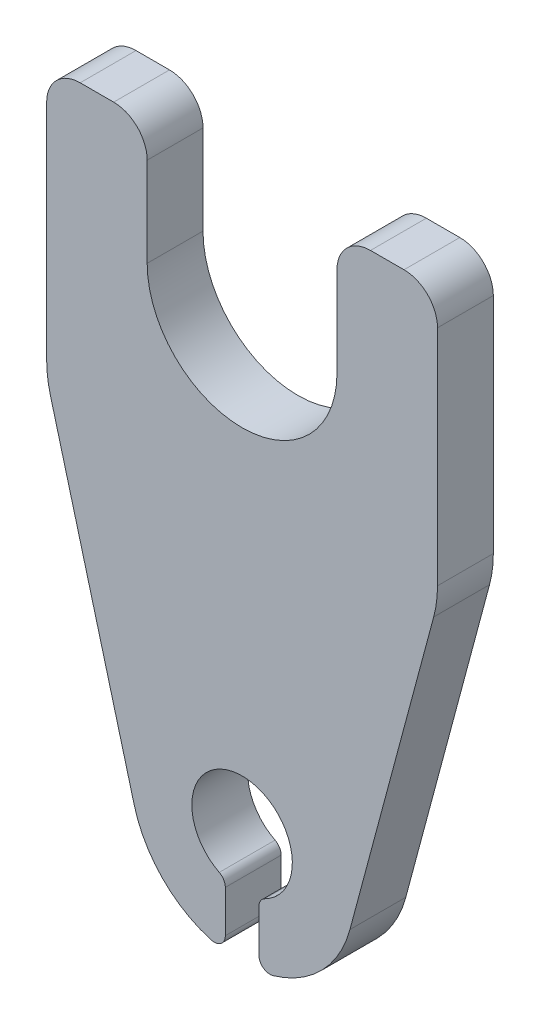
SolidWorks part; units mm, degrees
ref_plane "Plane1" through (0, 0, 0) normal (0, 0, 1) x (1, 0, 0)
ref_plane "Plane2" through (0, 0, 0) normal (0, 1, 0) x (1, 0, 0)
ref_plane "Plane3" through (0, 0, 0) normal (1, 0, 0) x (0, 0, -1)
sketch "Sketch1" plane through (0, 0, 0) normal (0, 0, 1) x (1, 0, 0)
  line L0 (0, 0) -> (0, 40) construction
  line L1 (1.5, -4.899) -> (1.5, -8.6458)
  line L2 (-1.5, -4.899) -> (-1.5, -8.6458)
  line L3 (8.5, 40) -> (8.5, 48)
  line L4 (11.5, 51) -> (14.5, 51)
  line L5 (-11.5, 51) -> (-14.5, 51)
  line L6 (-8.5, 40) -> (-8.5, 48)
  line L8 (17.5, 48) -> (17.5, 27.9904)
  line L9 (17.1593, 25.4022) -> (9.6593, -2.5882)
  line L10 (-17.1593, 25.4022) -> (-9.6593, -2.5882)
  line L11 (-17.5, 48) -> (-17.5, 27.9904)
  arc A0 (2.0455, -4.0083) -> (-2.0455, -4.0083) centre (0, 0) ccw
  arc A1 (2.7778, -9.6065) -> (9.6593, -2.5882) centre (0, 0) ccw
  arc A2 (-8.5, 40) -> (8.5, 40) centre (0, 40) ccw
  arc A3 (-9.6593, -2.5882) -> (-2.7778, -9.6065) centre (0, 0) ccw
  arc A4 (11.5, 51) -> (8.5, 48) centre (11.5, 48) ccw
  arc A5 (-8.5, 48) -> (-11.5, 51) centre (-11.5, 48) ccw
  arc A6 (-17.5, 48) -> (-14.5, 51) centre (-14.5, 48) cw
  arc A7 (17.5, 48) -> (14.5, 51) centre (14.5, 48) ccw
  arc A10 (-17.5, 27.9904) -> (-17.1593, 25.4022) centre (-7.5, 27.9904) ccw
  arc A11 (17.1593, 25.4022) -> (17.5, 27.9904) centre (7.5, 27.9904) ccw
  arc A12 (2.7778, -9.6065) -> (1.5, -8.6458) centre (2.5, -8.6458) cw
  arc A13 (2.0455, -4.0083) -> (1.5, -4.899) centre (2.5, -4.899) ccw
  arc A14 (-2.0455, -4.0083) -> (-1.5, -4.899) centre (-2.5, -4.899) cw
  arc A15 (-2.7778, -9.6065) -> (-1.5, -8.6458) centre (-2.5, -8.6458) ccw
  point P39 (-17.5, 26.6739)
  point P42 (17.5, 26.6739)
  point P45 (1.5, -9.8869)
  point P48 (1.5, -4.2426)
  point P51 (-1.5, -4.2426)
  point P54 (-1.5, -9.8869)
  dimension "D3" = 4.5
  dimension "D4" = 10
  dimension "D5" = 8.5
  dimension "D11" = 10
  dimension "D8" = 3
  dimension "D10" = 1
  dimension "D1" = 40
  dimension "D2" = 3
  dimension "D6" = 51
  dimension "D7" = 35
  dimension "D9" = 30
extrude "Base-Extrude" add sketch "Sketch1" along normal blind 5
